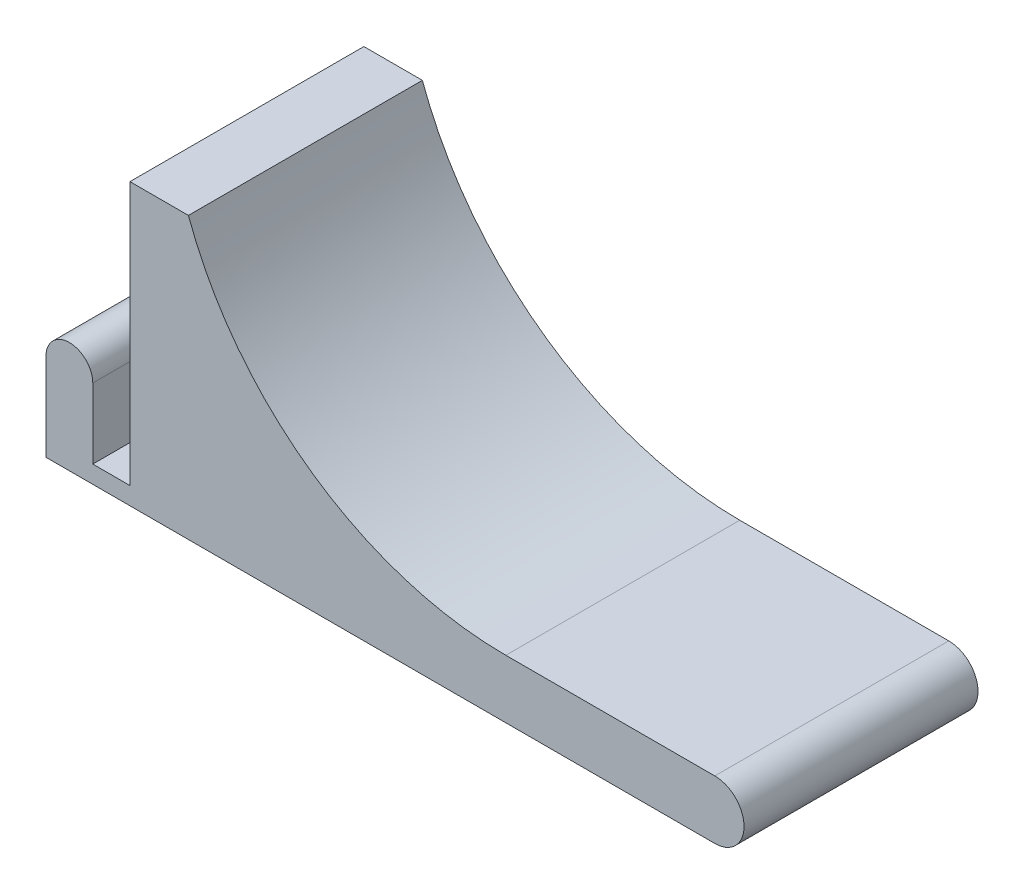
SolidWorks part; units mm, degrees
ref_plane "Front Plane" through (0, 0, 0) normal (0, 0, 1) x (1, 0, 0)
ref_plane "Top Plane" through (0, 0, 0) normal (0, 1, 0) x (1, 0, 0)
ref_plane "Right Plane" through (0, 0, 0) normal (1, 0, 0) x (0, 0, -1)
sketch "Sketch1" plane through (0, 0, 0) normal (0, 0, 1) x (1, 0, 0)
  line L0 (0, 15) -> (0, 0)
  line L1 (0, 0) -> (114.35, 0)
  line L2 (114.35, 10) -> (78.6196, 10)
  line L4 (14.35, 48) -> (14.35, 3)
  line L5 (14.35, 3) -> (8, 3)
  line L6 (8, 3) -> (8, 15)
  line L7 (14.35, 48) -> (24.35, 48)
  line L8 (24.35, 48) -> (37.9749, 10.5658) construction
  arc A0 (114.35, 0) -> (114.35, 10) centre (114.35, 5) ccw
  arc A1 (78.6196, 10) -> (24.35, 48) centre (78.6196, 67.7525) cw
  arc A3 (8, 15) -> (0, 15) centre (4, 15) ccw
  point P9 (23.6222, 27.8597)
  point P10 (0, 0)
  point P16 (24.35, 29.1102)
  point P18 (36.3066, 10)
  dimension "D9" = 20
  dimension "D1" = 6.35
  dimension "D2" = 3
  dimension "D3" = 8
  dimension "D4" = 15
  dimension "D5" = 10
  dimension "D6" = 10
  dimension "D7" = 45
  dimension "D8" = 100
extrude "Boss-Extrude1" add sketch "Sketch1" along normal blind 40
